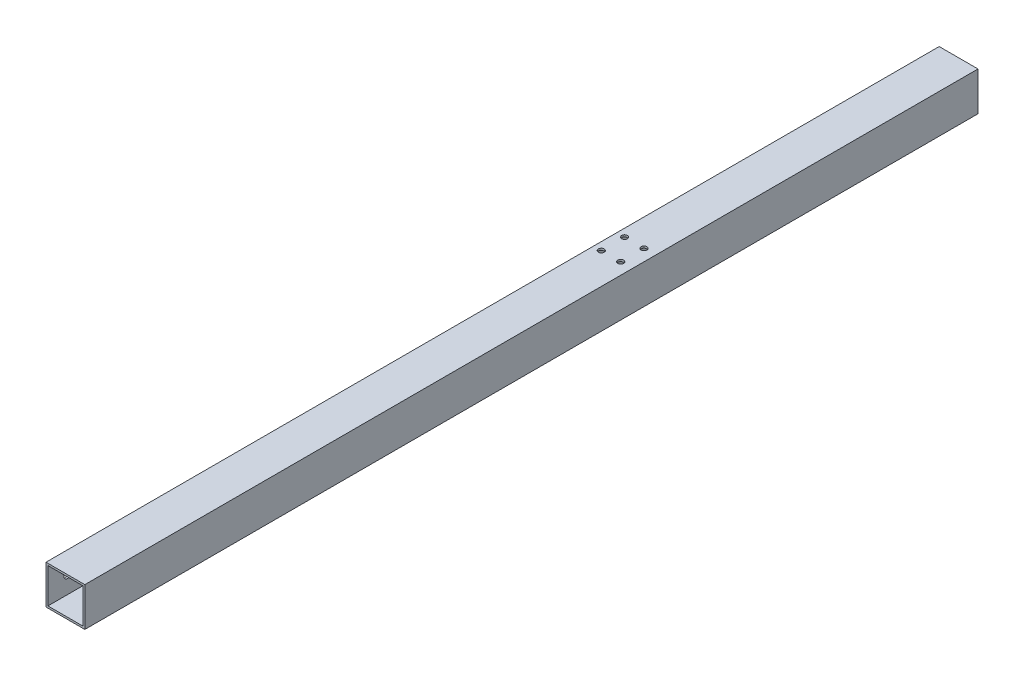
SolidWorks part; units mm, degrees
ref_plane "前视基准面" through (0, 0, 0) normal (0, 0, 1) x (1, 0, 0)
ref_plane "上视基准面" through (0, 0, 0) normal (0, 1, 0) x (1, 0, 0)
ref_plane "右视基准面" through (0, 0, 0) normal (1, 0, 0) x (0, 0, -1)
sketch "草图1" plane through (0, 0, 0) normal (0, 0, 1) x (1, 0, 0)
  line L1 (-10, 10) -> (10, 10)
  line L2 (-10, 10) -> (-10, -10)
  line L3 (-10, -10) -> (10, -10)
  line L4 (10, 10) -> (10, -10)
  line L5 (-10, 10) -> (10, -10) construction
  line L6 (-10, -10) -> (10, 10) construction
  line L7 (-9, 9) -> (9, 9)
  line L8 (-9, 9) -> (-9, -9)
  line L9 (-9, -9) -> (9, -9)
  line L10 (9, 9) -> (9, -9)
  line L11 (-9, 9) -> (9, -9) construction
  line L12 (-9, -9) -> (9, 9) construction
  point P0 (0, 0)
  point P6 (0, 0)
  dimension "D1" = 20
  dimension "D2" = 20
  dimension "D3" = 18
  dimension "D4" = 18
extrude "凸台-拉伸1" add sketch "草图1" along normal blind 460
sketch "草图2" plane through (-10, 0, 0) normal (-1, 0, 0) x (0, 0, 1)
  circle A0 centre (10, 0) radius 1.8
  dimension "D1" = 3.6
extrude "切除-拉伸1" cut sketch "草图2" against normal blind 3
sketch "草图3" plane through (-10, 0, 0) normal (-1, 0, 0) x (0, 0, 1)
  line L1 (0, 10) -> (0, -10) construction
  circle A0 centre (198, 0) radius 1.8
  dimension "D1" = 198
extrude "切除-拉伸2" cut sketch "草图3" against normal blind 3
sketch "草图5" plane through (-10, 0, 0) normal (-1, 0, 0) x (0, 0, 1)
  line L0 (460, 10) -> (460, -10) construction
  circle A0 centre (450, 0) radius 1.8
  dimension "D1" = 10
extrude "切除-拉伸3" cut sketch "草图5" against normal blind 3
sketch "草图6" plane through (-10, 0, 0) normal (-1, 0, 0) x (0, 0, 1)
  line L0 (460, 10) -> (460, -10) construction
  circle A0 centre (262, 0) radius 1.8
  dimension "D1" = 198
extrude "切除-拉伸4" cut sketch "草图6" against normal blind 10
sketch "草图7" plane through (0, 10, 0) normal (0, 1, 0) x (1, 0, 0)
  circle A0 centre (4, -166) radius 1.5
  circle A1 centre (-6, -166) radius 1.5
  circle A2 centre (4, -178) radius 1.5
  circle A3 centre (-6, -178) radius 1.5
extrude "切除-拉伸5" cut sketch "草图7" against normal blind 20
